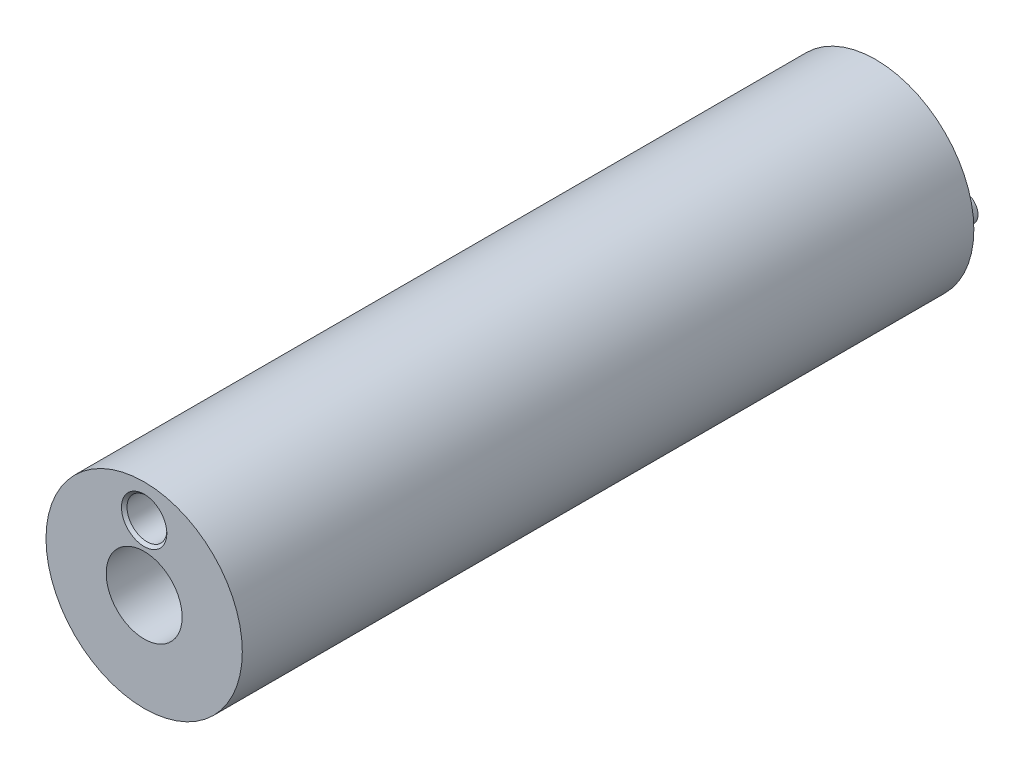
SolidWorks part; units mm, degrees
ref_plane "前视基准面" through (0, 0, 0) normal (0, 0, 1) x (1, 0, 0)
ref_plane "上视基准面" through (0, 0, 0) normal (0, 1, 0) x (1, 0, 0)
ref_plane "右视基准面" through (0, 0, 0) normal (1, 0, 0) x (0, 0, -1)
sketch "草图1" plane through (0, 0, 0) normal (0, 0, 1) x (1, 0, 0)
  circle A0 centre (0, 0) radius 10.6
  circle A1 centre (0, 7) radius 2.15
  circle A2 centre (0, 0) radius 4.1
extrude "凸台-拉伸1" add sketch "草图1" along normal blind 79
sketch "草图2" plane through (0, 0, 0) normal (0, 0, 1) x (1, 0, 0)
  circle A0 centre (-8, 0) radius 1.45
  circle A1 centre (8, 0) radius 1.45
extrude "凸台-拉伸2" add sketch "草图2" against normal blind 1.6
chamfer "倒角1" distance 0.3 angle 45 2 edges at (2.15, 7, 0) (2.15, 7, 79)
